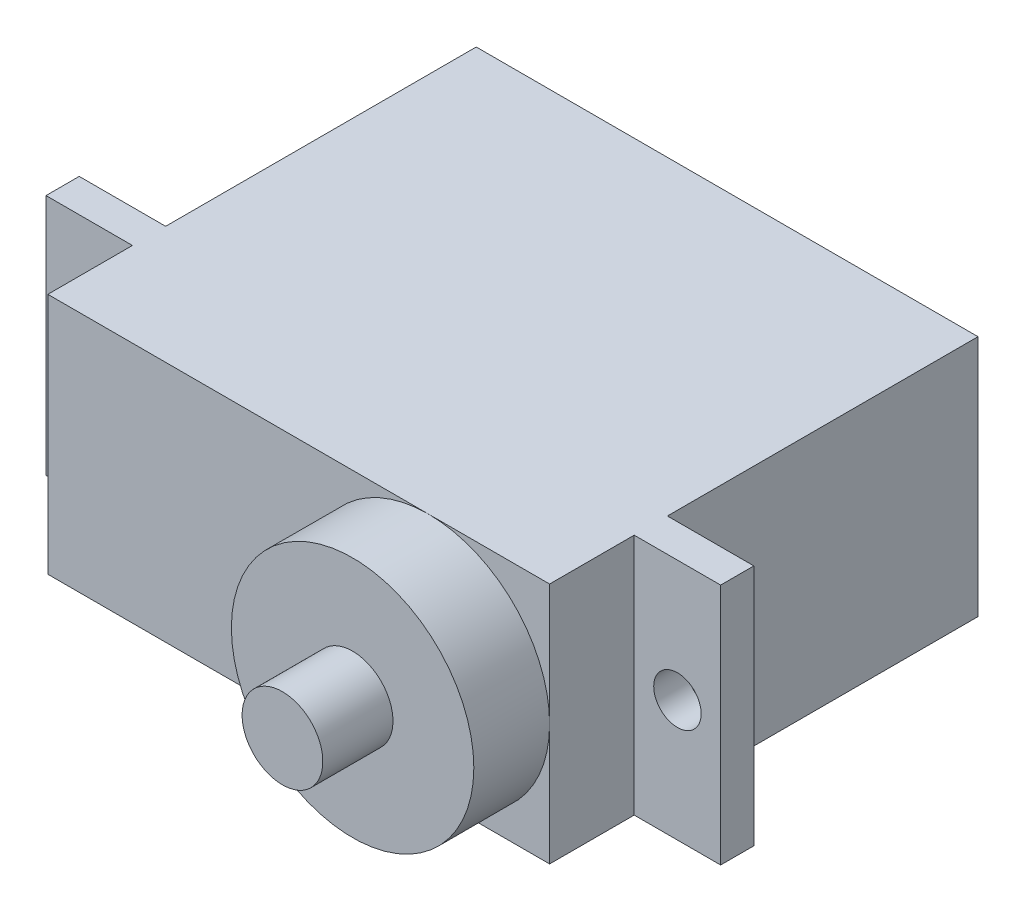
SolidWorks part; units mm, degrees
ref_plane "Front" through (0, 0, 0) normal (0, 0, 1) x (1, 0, 0)
ref_plane "Top" through (0, 0, 0) normal (0, 1, 0) x (1, 0, 0)
ref_plane "Right" through (0, 0, 0) normal (1, 0, 0) x (0, 0, -1)
sketch "Sketch1" plane through (0, 0, 0) normal (0, 0, 1) x (1, 0, 0)
  line L1 (-11.9, -5.75) -> (11.9, -5.75)
  line L2 (-11.9, -5.75) -> (-11.9, 5.75)
  line L3 (-11.9, 5.75) -> (11.9, 5.75)
  line L4 (11.9, -5.75) -> (11.9, 5.75)
  line L5 (-11.9, -5.75) -> (11.9, 5.75) construction
  line L6 (-11.9, 5.75) -> (11.9, -5.75) construction
  point P0 (0, 0)
  dimension "D1" = 23.8
  dimension "D2" = 11.5
extrude "Body" add sketch "Sketch1" along normal blind 20.32 contours L3 L4 L1 L2
ref_plane "ConnectorPlane" through (0, 0, 14.732) normal (0, 0, -1) x (-1, 0, 0)
sketch "Sketch2" plane through (0, 0, 14.732) normal (0, 0, -1) x (-1, 0, 0)
  line L0 (11.9, -5.75) -> (11.9, 5.75) construction
  line L1 (-11.9, -5.75) -> (-11.9, 5.75) construction
  line L2 (11.9, -5.75) -> (11.9, 5.75)
  line L3 (-11.9, -5.75) -> (-11.9, 5.75)
  line L4 (11.9, 5.75) -> (16, 5.75)
  line L5 (16, 5.75) -> (16, -5.75)
  line L6 (16, -5.75) -> (11.9, -5.75)
  line L7 (-11.9, 5.75) -> (-16, 5.75)
  line L8 (-16, 5.75) -> (-16, -5.75)
  line L9 (-16, -5.75) -> (-11.9, -5.75)
  line L10 (-16, 0) -> (-11.9, 0) construction
  line L11 (16, 0) -> (11.9, 0) construction
  circle A0 centre (-13.95, 0) radius 1.125
  circle A1 centre (13.95, 0) radius 1.125
  dimension "D2" = 2.25
  dimension "D1" = 32
extrude "Boss-Extrude2" add sketch "Sketch2" against normal blind 1.5748 contours L8 L9 L3 L7 | L6 L5 L4 L2 A1
ref_plane "Plane2" through (0, 0, 27.2415) normal (0, 0, -1) x (-1, 0, 0)
sketch "Sketch3" plane through (0, 0, 20.32) normal (0, 0, 1) x (1, 0, 0)
  line L0 (6.15, 5.75) -> (6.15, -5.75) construction
  line L1 (-11.9, 5.75) -> (11.9, 5.75) construction
  line L2 (-11.9, -5.75) -> (11.9, -5.75) construction
  line L4 (11.9, -5.75) -> (11.9, 5.75) construction
  circle A0 centre (6.15, 0) radius 1.915
  arc A1 (6.15, 5.75) -> (6.15, -5.75) centre (6.15, 0) cw
  dimension "D1" = 3.83
extrude "Boss-Extrude3" add sketch "Sketch3" along normal up to surface (6.9215 mm away) contours A0 up to plane "Plane2"
ref_plane "Plane1" through (0, 0, 23.9141) normal (0, 0, -1) x (-1, 0, 0)
sketch "Sketch4" plane through (0, 0, 20.32) normal (0, 0, 1) x (1, 0, 0)
  line L0 (11.9, -5.75) -> (11.9, 5.75) construction
  circle A0 centre (6.15, 0) radius 5.75
  circle A1 centre (6.15, 0) radius 1.915 construction
extrude "Boss-Extrude4" add sketch "Sketch4" along normal up to surface (3.5941 mm away) up to plane "Plane1"
